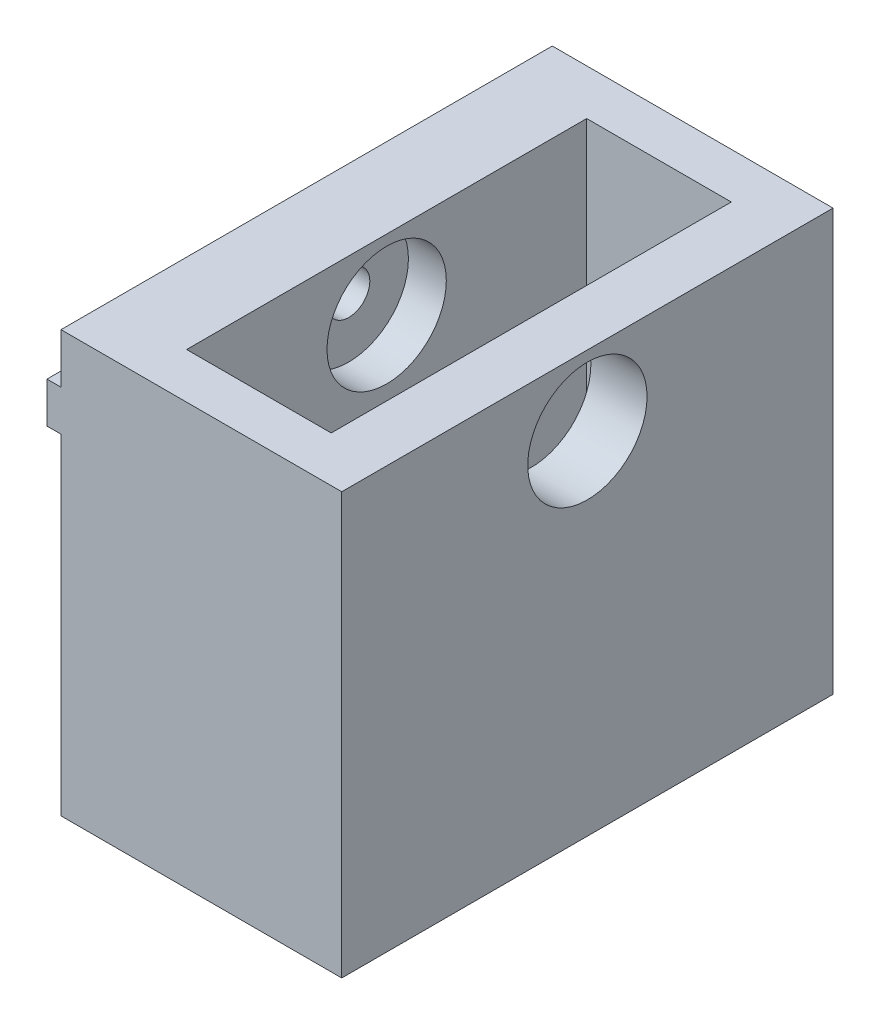
SolidWorks part; units mm, degrees
ref_plane "Front Plane" through (0, 0, 0) normal (0, 0, 1) x (1, 0, 0)
ref_plane "Top Plane" through (0, 0, 0) normal (0, 1, 0) x (1, 0, 0)
ref_plane "Right Plane" through (0, 0, 0) normal (1, 0, 0) x (0, 0, -1)
ref_plane "Plane1" through (3, 0, 0) normal (1, 0, 0) x (0, 0, -1)
sketch "Sketch1" plane through (0, 0, 0) normal (0, 0, 1) x (1, 0, 0)
  line L0 (-1, 26.45) -> (-1, 23.55)
  line L1 (-1, 23.55) -> (0, 23.55)
  line L2 (0, 23.55) -> (0, 0)
  line L5 (0, 0) -> (20, 0)
  line L6 (20, 0) -> (20, 30)
  line L7 (20, 30) -> (0, 30)
  line L8 (0, 30) -> (0, 26.45)
  line L9 (0, 26.45) -> (-1, 26.45)
  point P5 (2, 0)
  point P6 (2, -11.7695)
  point P8 (2, -11.4091)
  point P12 (0, 0)
  dimension "D1" = 2.9
  dimension "D2" = 3.55
  dimension "D3" = 1
  dimension "D4" = 20
  dimension "D5" = 30
extrude "Main" add sketch "Sketch1" along normal mid plane 35
sketch "Sketch2" plane through (0, 30, 0) normal (0, 1, 0) x (1, 0, 0)
  line L0 (20, 17.5) -> (0, 17.5) construction
  line L1 (5.7, 14.25) -> (16, 14.25)
  line L2 (5.7, 14.25) -> (5.7, -14.25)
  line L3 (5.7, -14.25) -> (16, -14.25)
  line L4 (16, 14.25) -> (16, -14.25)
  line L5 (20, -17.5) -> (0, -17.5) construction
  line L6 (20, -17.5) -> (20, 17.5) construction
  line L7 (0, -17.5) -> (0, 17.5) construction
  dimension "D1" = 28.5
  dimension "D2" = 3.25
  dimension "D3" = 3.25
  dimension "D4" = 10.3
  dimension "D5" = 4
  dimension "D6" = 5.7
extrude "HoleForSwitch" cut sketch "Sketch2" against normal through all
sketch "Sketch4" plane through (-1, 0, 0) normal (-1, 0, 0) x (0, 0, 1)
  line L0 (17.5, 30) -> (-17.5, 30) construction
  circle A0 centre (0, 25) radius 1.5
  point P4 (0, 0)
  dimension "D1" = 3
  dimension "D2" = 5
extrude "MakerBeamFixHole" cut sketch "Sketch4" against normal through all
sketch "Sketch5" plane through (20, 0, 0) normal (1, 0, 0) x (0, 0, -1)
  circle A0 centre (0, 25) radius 4.25
  circle A1 centre (0, 25) radius 1.5 construction
  dimension "D1" = 8.5
extrude "HoleForTool" cut sketch "Sketch5" against normal up to surface (17 mm away)
